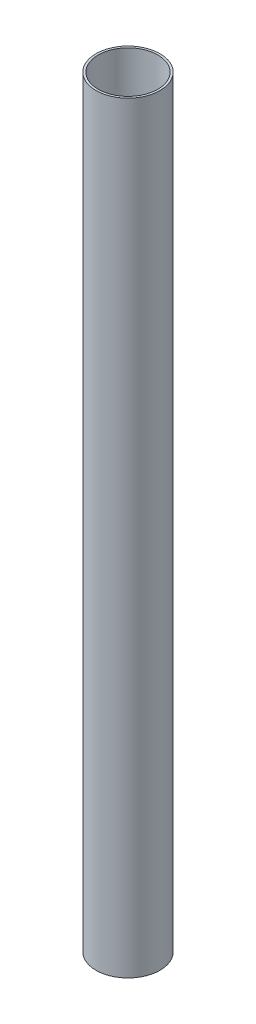
SolidWorks part; units mm, degrees
ref_plane "Front Plane" through (0, 0, 0) normal (0, 0, 1) x (1, 0, 0)
ref_plane "Top Plane" through (0, 0, 0) normal (0, 1, 0) x (1, 0, 0)
ref_plane "Right Plane" through (0, 0, 0) normal (1, 0, 0) x (0, 0, -1)
sketch "Sketch1" plane through (0, 0, 0) normal (0, 1, 0) x (1, 0, 0)
  circle A0 centre (0, 0) radius 27.3685
  circle A1 centre (0, 0) radius 29.3685
  dimension "D1" = 54.737
  dimension "D2" = 2
extrude "Boss-Extrude1" add sketch "Sketch1" along normal blind 700
